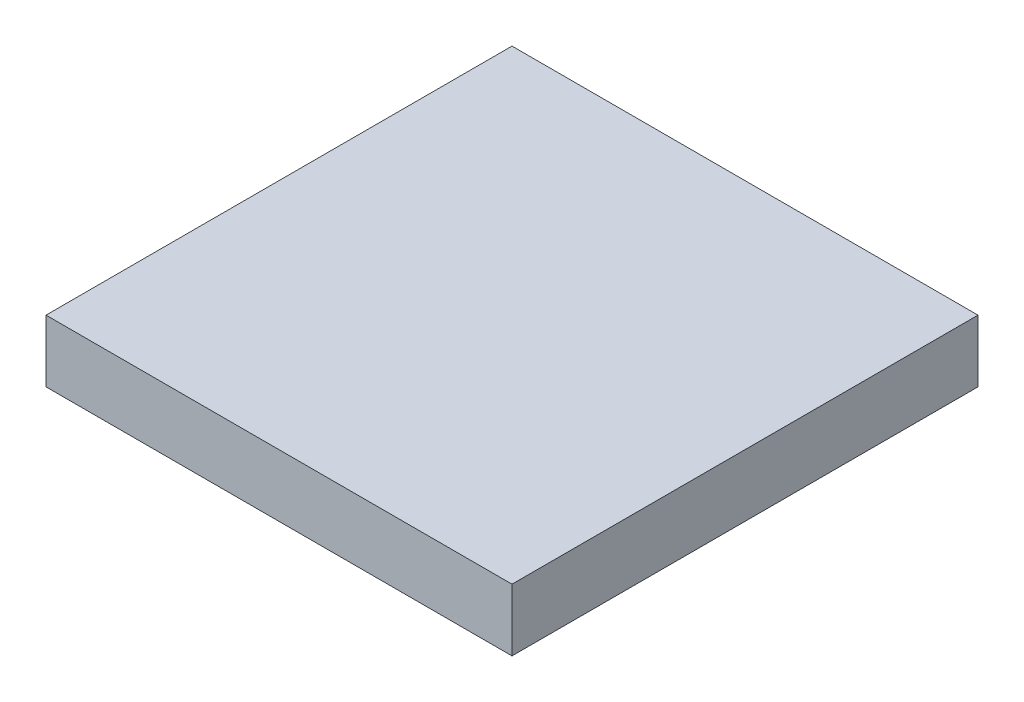
SolidWorks part; units mm, degrees
ref_plane "Front Plane" through (0, 0, 0) normal (0, 0, 1) x (1, 0, 0)
ref_plane "Top Plane" through (0, 0, 0) normal (0, 1, 0) x (1, 0, 0)
ref_plane "Right Plane" through (0, 0, 0) normal (1, 0, 0) x (0, 0, -1)
sketch "Sketch1" plane through (0, 0, 0) normal (0, 1, 0) x (1, 0, 0)
  line L1 (0, 0) -> (75, 0)
  line L2 (0, 0) -> (0, 75)
  line L3 (0, 75) -> (75, 75)
  line L4 (75, 0) -> (75, 75)
extrude "Boss-Extrude1" add sketch "Sketch1" along normal blind 10
